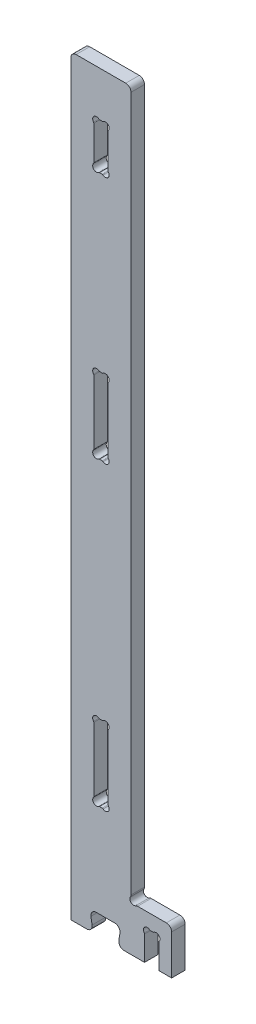
SolidWorks part; units mm, degrees
ref_plane "Front Plane" through (0, 0, 0) normal (0, 0, 1) x (1, 0, 0)
ref_plane "Top Plane" through (0, 0, 0) normal (0, 1, 0) x (1, 0, 0)
ref_plane "Right Plane" through (0, 0, 0) normal (1, 0, 0) x (0, 0, -1)
sketch "Sketch1" plane through (0, 0, 0) normal (0, 0, 1) x (1, 0, 0)
  line L0 (131, 60) -> (131, 0) construction
  line L1 (0, 0) -> (29.4936, 0)
  line L2 (0, 0) -> (0, 1000)
  line L3 (0, 1000) -> (80, 1000)
  line L4 (80, 68.7456) -> (80, 1000)
  line L5 (88.7456, 60) -> (134, 60)
  line L6 (62.5064, 0) -> (134, 0)
  line L7 (30, 0) -> (30, 25) construction
  line L8 (134, 60) -> (134, 0)
  line L9 (30, 0) -> (26, 25) construction
  line L10 (26, 25) -> (66, 25) construction
  line L11 (62, 0) -> (66, 25) construction
  line L12 (62, 0) -> (62, 25) construction
  line L13 (80, 60) -> (83.5355, 63.5355) construction
  line L14 (29.4936, 0) -> (25.4136, 25.5)
  line L15 (25.4136, 25.5) -> (66.5864, 25.5)
  line L16 (62.5064, 0) -> (66.5864, 25.5)
  line L18 (29.5063, -0.079) -> (25.4136, 25.5) construction
  line L19 (62.4937, -0.079) -> (66.5864, 25.5) construction
  arc A0 (79.2678, 66.1406) -> (86.1406, 59.2678) centre (83.5355, 63.5355) ccw
  arc A1 (79.2678, 66.1406) -> (80, 68.7456) centre (75, 68.7456) ccw
  arc A2 (86.1406, 59.2678) -> (88.7456, 60) centre (88.7456, 55) cw
  dimension "D12" = 5
  dimension "D13" = 5
  dimension "D2" = 1000
  dimension "D3" = 54
  dimension "D4" = 60
  dimension "D6" = 30
  dimension "D9" = 40
  dimension "D10" = 45
  dimension "D11" = 80
  dimension "D5" = 25
  dimension "D14" = 80.91
  dimension "D8" = 80.91
extrude "Boss-Extrude1" add sketch "Sketch1" along normal blind 18 contours L1 L14 L15 L16 L6 L8 L5 A2 A0 A1 L4 L3 L2
sketch "Sketch2" plane through (0, 0, 0) normal (0, 0, 1) x (1, 0, 0)
  line L0 (40, 60) -> (40, 549.5) construction
  line L1 (80, 68.7456) -> (80, 1000) construction
  line L2 (0, 0) -> (0, 1000) construction
  line L3 (88.7456, 60) -> (134, 60) construction
  line L4 (0, 1000) -> (80, 1000) construction
  line L5 (30.5, 600) -> (49.5, 600) construction
  line L6 (30.5, 642.7488) -> (30.5, 557.2512)
  line L7 (38.2512, 549.5) -> (41.7488, 549.5)
  line L8 (49.5, 642.7488) -> (49.5, 557.2512)
  line L9 (30.5, 549.5) -> (40, 559) construction
  line L10 (38.2512, 650.5) -> (41.7488, 650.5)
  line L16 (80, 60) -> (0, 60) construction
  arc A0 (30.1123, 556.1353) -> (37.1353, 549.1123) centre (34.0355, 553.0355) ccw
  arc A1 (42.8647, 549.1123) -> (41.7488, 549.5) centre (41.7488, 547.7) ccw
  arc A2 (49.8877, 556.1353) -> (42.8647, 549.1123) centre (45.9645, 553.0355) cw
  arc A3 (49.8877, 556.1353) -> (49.5, 557.2512) centre (51.3, 557.2512) cw
  arc A7 (30.1123, 556.1353) -> (30.5, 557.2512) centre (28.7, 557.2512) ccw
  arc A8 (37.1353, 549.1123) -> (38.2512, 549.5) centre (38.2512, 547.7) cw
  arc A9 (49.8877, 643.8647) -> (49.5, 642.7488) centre (51.3, 642.7488) ccw
  arc A10 (49.8877, 643.8647) -> (42.8647, 650.8877) centre (45.9645, 646.9645) ccw
  arc A11 (42.8647, 650.8877) -> (41.7488, 650.5) centre (41.7488, 652.3) cw
  arc A12 (37.1353, 650.8877) -> (38.2512, 650.5) centre (38.2512, 652.3) ccw
  arc A13 (30.1123, 643.8647) -> (37.1353, 650.8877) centre (34.0355, 646.9645) cw
  arc A14 (30.1123, 643.8647) -> (30.5, 642.7488) centre (28.7, 642.7488) cw
  point P21 (40, 549.5)
  point P36 (30.5, 556.5711)
  point P39 (37.5711, 549.5)
  dimension "D7" = 5
  dimension "D4" = 1.8
  dimension "D3" = 45
  dimension "D6" = 9.5
  dimension "D1" = 50.5
  dimension "D2" = 400
extrude "Cut-Extrude1" cut sketch "Sketch2" along normal through all
sketch "Sketch3" plane through (0, 0, 0) normal (0, 0, 1) x (1, 0, 0)
  line L0 (107.5, 60) -> (107.5, 0) construction
  line L1 (62.5064, 0) -> (134, 0) construction
  line L2 (98, 0) -> (117, 0)
  line L3 (117, 32.7488) -> (117, 0)
  line L4 (117, 40.5) -> (107.5, 31) construction
  line L5 (105.7512, 40.5) -> (109.2488, 40.5)
  line L7 (98, 32.7488) -> (98, 0)
  line L8 (80, 68.7456) -> (80, 1000) construction
  line L11 (88.7456, 60) -> (134, 60) construction
  arc A0 (117, 32.7488) -> (117.3877, 33.8647) centre (118.8, 32.7488) cw
  arc A1 (117.3877, 33.8647) -> (110.3647, 40.8877) centre (113.4645, 36.9645) ccw
  arc A2 (109.2488, 40.5) -> (110.3647, 40.8877) centre (109.2488, 42.3) ccw
  arc A3 (98, 32.7488) -> (97.6123, 33.8647) centre (96.2, 32.7488) ccw
  arc A4 (97.6123, 33.8647) -> (104.6353, 40.8877) centre (101.5355, 36.9645) cw
  arc A5 (105.7512, 40.5) -> (104.6353, 40.8877) centre (105.7512, 42.3) cw
  point P23 (107.5, 40.5)
  dimension "D3" = 5
  dimension "D5" = 1.8
  dimension "D1" = 45
  dimension "D2" = 9.5
  dimension "D4" = 40.5
  dimension "D6" = 18
extrude "Cut-Extrude2" cut sketch "Sketch3" along normal through all
sketch "Sketch4" plane through (0, 0, 0) normal (0, 0, 1) x (1, 0, 0)
  line L0 (30.5, 910) -> (40, 910) construction
  line L1 (30.5, 932.7488) -> (30.5, 887.2512)
  line L2 (38.2512, 879.5) -> (41.7488, 879.5)
  line L3 (0, 1000) -> (80, 1000) construction
  line L4 (30.5, 879.5) -> (40, 889) construction
  line L5 (49.5, 932.7488) -> (49.5, 887.2512)
  line L6 (38.2512, 940.5) -> (41.7488, 940.5)
  line L9 (40, 1000) -> (40, 879.5) construction
  arc A0 (30.1123, 886.1353) -> (37.1353, 879.1123) centre (34.0355, 883.0355) ccw
  arc A1 (38.2512, 879.5) -> (37.1353, 879.1123) centre (38.2512, 877.7) ccw
  arc A2 (30.5, 887.2512) -> (30.1123, 886.1353) centre (28.7, 887.2512) cw
  arc A3 (41.7488, 879.5) -> (42.8647, 879.1123) centre (41.7488, 877.7) cw
  arc A4 (49.8877, 886.1353) -> (42.8647, 879.1123) centre (45.9645, 883.0355) cw
  arc A5 (49.5, 887.2512) -> (49.8877, 886.1353) centre (51.3, 887.2512) ccw
  arc A6 (49.5, 932.7488) -> (49.8877, 933.8647) centre (51.3, 932.7488) cw
  arc A7 (49.8877, 933.8647) -> (42.8647, 940.8877) centre (45.9645, 936.9645) ccw
  arc A8 (41.7488, 940.5) -> (42.8647, 940.8877) centre (41.7488, 942.3) ccw
  arc A9 (38.2512, 940.5) -> (37.1353, 940.8877) centre (38.2512, 942.3) cw
  arc A10 (30.1123, 933.8647) -> (37.1353, 940.8877) centre (34.0355, 936.9645) cw
  arc A11 (30.5, 932.7488) -> (30.1123, 933.8647) centre (28.7, 932.7488) ccw
  point P16 (40, 879.5)
  point P23 (49.5, 910)
  point P24 (49.5, 910)
  dimension "D3" = 5
  dimension "D1" = 45
  dimension "D6" = 1.8
  dimension "D4" = 30.5
  dimension "D5" = 9.5
  dimension "D2" = 90
extrude "Cut-Extrude3" cut sketch "Sketch4" along normal through all
pattern_linear "LPattern1" count 2 spacing 400 along (0, -1, 0) of "Cut-Extrude1"
fillet "Fillet1" radius 7 7 edges at (134, 60, 9) (0, 1000, 9) (80, 1000, 9) (62.5064, 0, 9) (66.5864, 25.5, 9) (25.4136, 25.5, 9) (29.4936, 0, 9)
equation "\"tool_diameter\"=9"
equation "\"hole_clearance\"=0.5"
equation "\"material_thickness\"=18"
equation "\"clearance\"=0.5"
equation "\"outer_slot\"=0.5"
equation "\"fillet\"=7"
equation "\"D3@Sketch1\"=\"material_thickness\"*3"
equation "\"D12@Sketch1\"=\"tool_diameter\"/2+\"hole_clearance\""
equation "\"D13@Sketch1\"=\"D12@Sketch1\""
equation "\"D7@Sketch1\"=\"clearance\""
equation "\"D1@Boss-Extrude1\"=\"material_thickness\""
equation "\"D6@Sketch2\"=\"material_thickness\"/2+\"clearance\""
equation "\"D1@Sketch2\"=\"clearance\"+50"
equation "\"D7@Sketch2\"=\"tool_diameter\"/2+\"hole_clearance\""
equation "\"D4@Sketch2\"=\"material_thickness\"/10"
equation "\"D4@Sketch3\"=\"clearance\"+40"
equation "\"D2@Sketch3\"=\"material_thickness\"/2+\"clearance\""
equation "\"D3@Sketch3\"=\"tool_diameter\"/2+\"hole_clearance\""
equation "\"D5@Sketch3\"=\"material_thickness\"/10"
equation "\"D6@Sketch3\"=\"material_thickness\""
equation "\"D5@Sketch4\"=\"material_thickness\"/2+\"clearance\""
equation "\"D3@Sketch4\"=\"tool_diameter\"/2+\"hole_clearance\""
equation "\"D4@Sketch4\"=\"clearance\"+30"
equation "\"D6@Sketch4\"=\"material_thickness\"/10"
equation "\"D1@Fillet1\"=\"fillet\""
equation "\"D1@Fillet2\"=\"fillet\"+\"clearance\""
equation "\"string\"= 2 * \"tool_diameter\" / 2 * cos ( 45deg )"
equation "\"angle\"= IIF ( \"string\" < \"limit\" , 45 , ( 180 - 2 * arcsin ( \"ThicknessVStool_dia\" ) ) / 2 )"
equation "\"limit\"= \"material_thickness\" / 2 * 9 / 10"
equation "\"ThicknessVStool_dia\"= IIF ( \"limit\" / \"tool_diameter\" > 1 , 1 , \"limit\" / \"tool_diameter\" )"
equation "\"D3@Sketch2\"=\"angle\""
equation "\"D1@Sketch3\"=\"angle\""
equation "\"D1@Sketch4\"=\"angle\""
